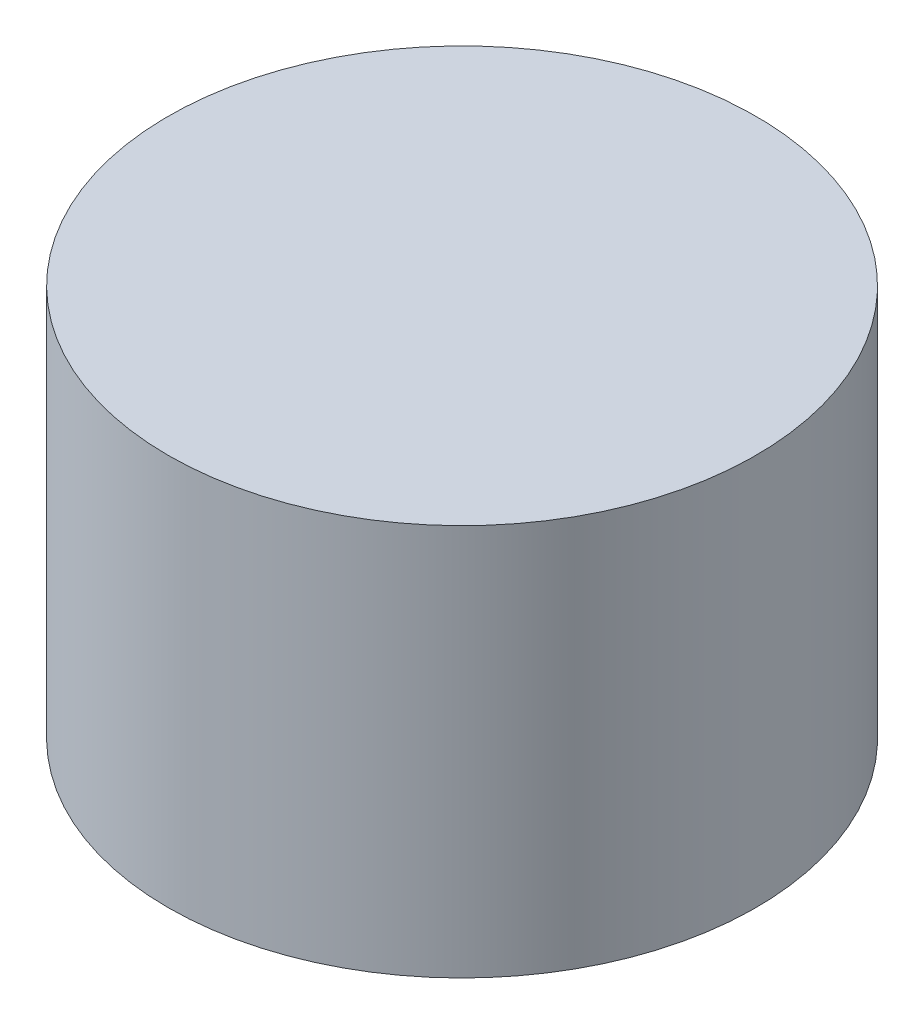
SolidWorks part; units mm, degrees
ref_plane "Front Plane" through (0, 0, 0) normal (0, 0, 1) x (1, 0, 0)
ref_plane "Top Plane" through (0, 0, 0) normal (0, 1, 0) x (1, 0, 0)
ref_plane "Right Plane" through (0, 0, 0) normal (1, 0, 0) x (0, 0, -1)
sketch "Sketch1" plane through (0, 0, 0) normal (0, 1, 0) x (1, 0, 0)
  circle A0 centre (0, 0) radius 150
extrude "Boss-Extrude1" add sketch "Sketch1" along normal blind 200 contours A0
